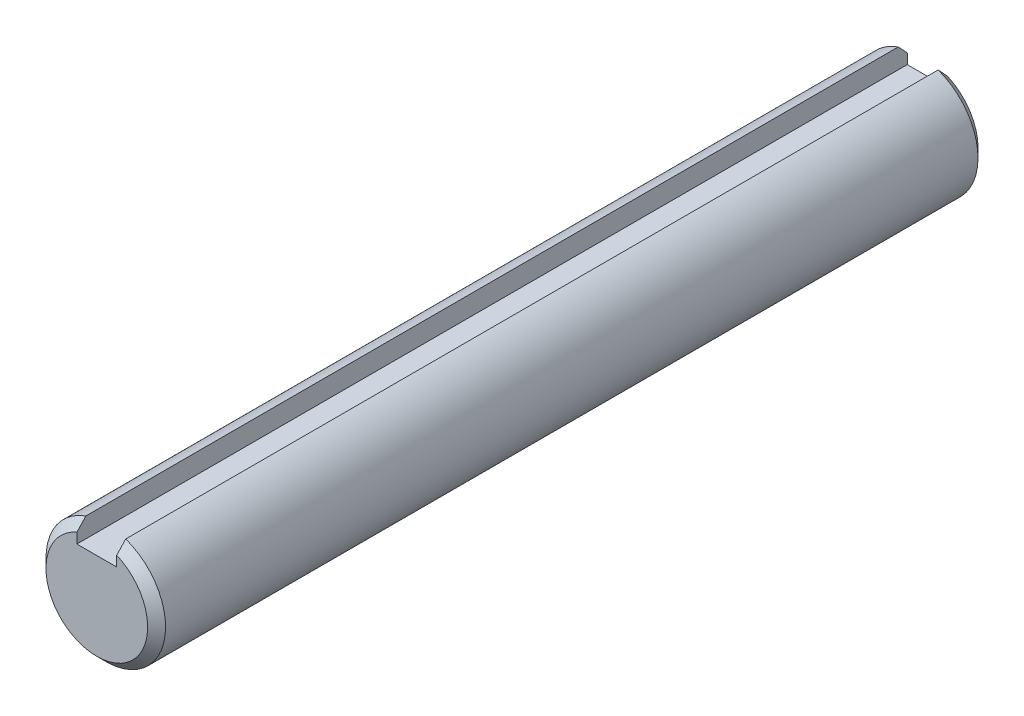
SolidWorks part; units mm, degrees
ref_plane "Front" through (0, 0, 0) normal (0, 0, 1) x (1, 0, 0)
ref_plane "Top" through (0, 0, 0) normal (0, 1, 0) x (1, 0, 0)
ref_plane "Right" through (0, 0, 0) normal (1, 0, 0) x (0, 0, -1)
sketch "Sketch1" plane through (0, 0, 0) normal (0, 0, 1) x (1, 0, 0)
  circle A0 centre (0, 0) radius 9
  dimension "dia" = 18
extrude "Extrude1" add sketch "Sketch1" along normal mid plane 125
sketch "Sketch2" plane through (0, 0, 0) normal (1, 0, 0) x (0, 0, -1)
  point P0 (-62.5, 9)
  point P1 (62.5, 9)
  point P2 (62.5, -9)
chamfer "Chamfer1" distance 1.35 angle 45 2 edges at (9, 0, -62.5) (9, 0, 62.5)
sketch "Sketch3" plane through (0, 0, 0) normal (0, 0, 1) x (1, 0, 0)
  line L1 (-3, 9) -> (3, 9)
  line L2 (-3, 9) -> (-3, 5.5)
  line L3 (-3, 5.5) -> (3, 5.5)
  line L4 (3, 9) -> (3, 5.5)
  dimension "key wd" = 6
  dimension "key dp" = 3.5
extrude "Extrude2" cut sketch "Sketch3" against normal through all and the other way through all
equation "\"D1@Chamfer1\" = \"dia@Sketch1\" * .075"
